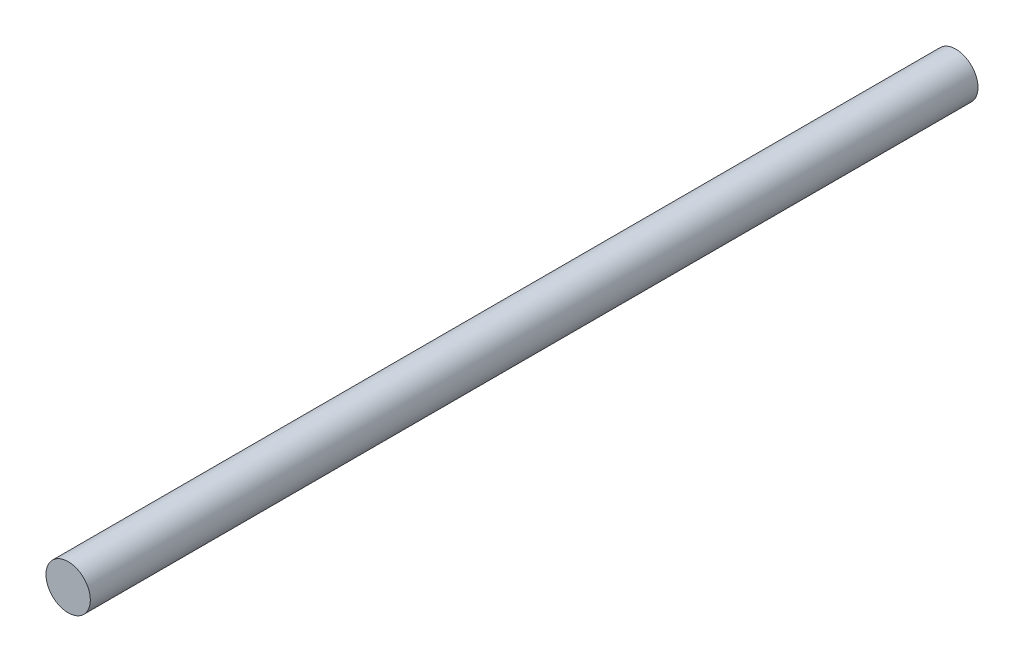
SolidWorks part; units mm, degrees
ref_plane "Front Plane" through (0, 0, 0) normal (0, 0, 1) x (1, 0, 0)
ref_plane "Top Plane" through (0, 0, 0) normal (0, 1, 0) x (1, 0, 0)
ref_plane "Right Plane" through (0, 0, 0) normal (1, 0, 0) x (0, 0, -1)
sketch "Sketch2" plane through (0, 0, 0) normal (0, 0, 1) x (1, 0, 0)
  circle A0 centre (0, 0) radius 10
  dimension "D1" = 20
extrude "Boss-Extrude1" add sketch "Sketch2" along normal mid plane 400
